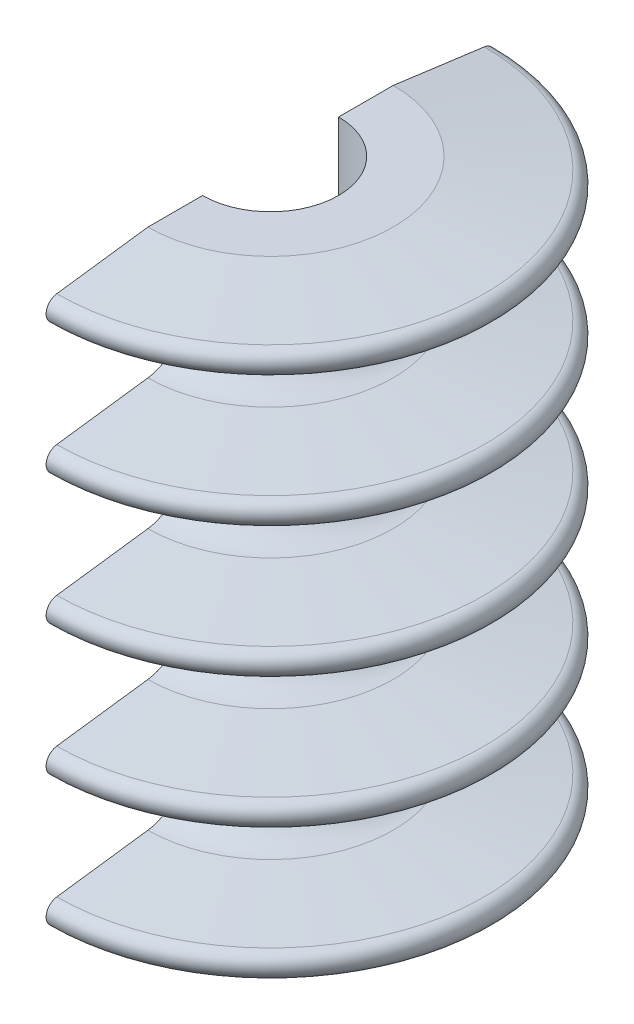
SolidWorks part; units mm, degrees
ref_plane "Front Plane" through (0, 0, 0) normal (0, 0, 1) x (1, 0, 0)
ref_plane "Top Plane" through (0, 0, 0) normal (0, 1, 0) x (1, 0, 0)
ref_plane "Right Plane" through (0, 0, 0) normal (1, 0, 0) x (0, 0, -1)
sketch "Sketch2" plane through (0, 0, 0) normal (0, 0, 1) x (1, 0, 0)
  line L0 (0, 47) -> (0, -47) construction
  line L1 (0, 47) -> (-20.2, 47) construction
  line L2 (-20.2, 47) -> (-35.2, 45)
  line L3 (-35.2, 45) -> (-35.2, 41) construction
  line L4 (-35.2, 41) -> (-20.2, 39)
  line L5 (-35.2, 43) -> (0, 43) construction
  line L6 (-20.2, 39) -> (-20.2, 25.5) construction
  line L7 (-20.2, 25.5) -> (-35.2, 23.5)
  line L8 (-20.2, 47) -> (-11.2, 47)
  line L9 (-35.2, 23.5) -> (-35.2, 19.5) construction
  line L10 (-35.2, 19.5) -> (-20.2, 17.5)
  line L11 (-20.2, 17.5) -> (-20.2, 4) construction
  line L12 (-20.2, 4) -> (-35.2, 2)
  line L13 (-20.2, -47) -> (-11.2, -47)
  line L14 (-35.2, 2) -> (-35.2, -2) construction
  line L15 (-35.2, -2) -> (-20.2, -4)
  line L16 (-20.2, -4) -> (-20.2, -17.5) construction
  line L17 (-20.2, -17.5) -> (-35.2, -19.5)
  line L18 (-11.2, 47) -> (-11.2, -47)
  line L19 (-35.2, -19.5) -> (-35.2, -23.5) construction
  line L20 (-35.2, -23.5) -> (-20.2, -25.5)
  line L21 (-20.2, -25.5) -> (-20.2, -39) construction
  line L22 (-20.2, -39) -> (-35.2, -41)
  line L24 (-35.2, -41) -> (-35.2, -45) construction
  line L25 (-35.2, -45) -> (-20.2, -47)
  line L27 (-20.2, -47) -> (0, -47) construction
  line L28 (0, 25.5) -> (-20.2, 25.5) [skipped]
  line L29 (0, 4) -> (-20.2, 4) [skipped]
  line L30 (0, -17.5) -> (-20.2, -17.5) [skipped]
  line L31 (0, -39) -> (-20.2, -39) [skipped]
  line L32 (-20.2, -47) -> (-20.2, -60.5) construction
  arc A0 (-35.2, 45) -> (-35.2, 41) centre (-34.9333, 43) ccw
  arc A1 (-20.2, 39) -> (-20.2, 25.5) centre (-21.1, 32.25) cw
  arc A2 (-35.2, 23.5) -> (-35.2, 19.5) centre (-34.9333, 21.5) ccw
  arc A3 (-20.2, 17.5) -> (-20.2, 4) centre (-21.1, 10.75) cw
  arc A4 (-35.2, 2) -> (-35.2, -2) centre (-34.9333, 0) ccw
  arc A5 (-20.2, -4) -> (-20.2, -17.5) centre (-21.1, -10.75) cw
  arc A6 (-35.2, -19.5) -> (-35.2, -23.5) centre (-34.9333, -21.5) ccw
  arc A7 (-20.2, -25.5) -> (-20.2, -39) centre (-21.1, -32.25) cw
  arc A8 (-35.2, -41) -> (-35.2, -45) centre (-34.9333, -43) ccw
  arc A10 (-20.2, -47) -> (-20.2, -60.5) centre (-21.1, -53.75) cw [skipped]
  point P4 (0, 0)
  point P43 (-20.2, 32.25)
  dimension "D1" = 94
  dimension "D2" = 11.2
  dimension "D3" = 15
  dimension "D4" = 4
  dimension "D5" = 4
  dimension "D6" = 5
  dimension "D8" = 9
  dimension "7" = 4
  dimension "D10" = 9
  dimension "D9" = 5
revolve "Revolve1" add sketch "Sketch2" angle 360 about L0
sketch "Sketch3" plane through (0, -47, 0) normal (0, -1, 0) x (1, 0, 0)
  line L1 (0, -55.1346) -> (-63.7941, -55.1346)
  line L2 (0, -55.1346) -> (0, 55.0005)
  line L3 (0, 55.0005) -> (-63.7941, 55.0005)
  line L4 (-63.7941, -55.1346) -> (-63.7941, 55.0005)
extrude "Cut-Extrude1" cut sketch "Sketch3" against normal up to surface (94 mm away) up to face at (-11.2, 47, 0)
sketch "Sketch4" plane through (0, 0, 0) normal (1, 0, 0) x (0, 0, -1)
  circle A0 centre (0, -32.25) radius 1.7
  circle A1 centre (0, 32.25) radius 1.7
  arc A2 (-20.2, -39) -> (-20.2, -25.5) centre (-21.1, -32.25) ccw construction
  arc A3 (-20.2, 25.5) -> (-20.2, 39) centre (-21.1, 32.25) ccw construction
  point P11 (-14.2903, -32.25)
  point P16 (-14.2903, 32.25)
  dimension "D1" = 3.4
extrude "Cut-Extrude2" cut sketch "Sketch4" along normal through all
ref_plane "Plane1" through (17, 0, 0) normal (1, 0, 0) x (0, 0, -1)
sketch "Sketch5" plane through (17, 0, 0) normal (1, 0, 0) x (0, 0, -1)
  line L1 (-2.95, -30.5468) -> (-2.95, -33.9532)
  line L2 (-2.95, -33.9532) -> (0, -35.6564)
  line L3 (0, -35.6564) -> (2.95, -33.9532)
  line L4 (2.95, -33.9532) -> (2.95, -30.5468)
  line L5 (2.95, -30.5468) -> (0, -28.8436)
  line L6 (0, -28.8436) -> (-2.95, -30.5468)
  line L7 (-2.95, 30.5468) -> (0, 28.8436)
  line L8 (0, 28.8436) -> (2.95, 30.5468)
  line L9 (2.95, 30.5468) -> (2.95, 33.9532)
  line L10 (2.95, 33.9532) -> (0, 35.6564)
  line L11 (0, 35.6564) -> (-2.95, 33.9532)
  line L12 (-2.95, 33.9532) -> (-2.95, 30.5468)
  circle A0 centre (0, -32.25) radius 2.95 construction
  circle A1 centre (0, 32.25) radius 2.95 construction
  circle A2 centre (0, -32.25) radius 2.95 construction
  circle A3 centre (0, 32.25) radius 2.95 construction
  dimension "D1" = 5.9
  dimension "D2" = 5.9
extrude "Cut-Extrude3" cut sketch "Sketch5" against normal blind 3.8
